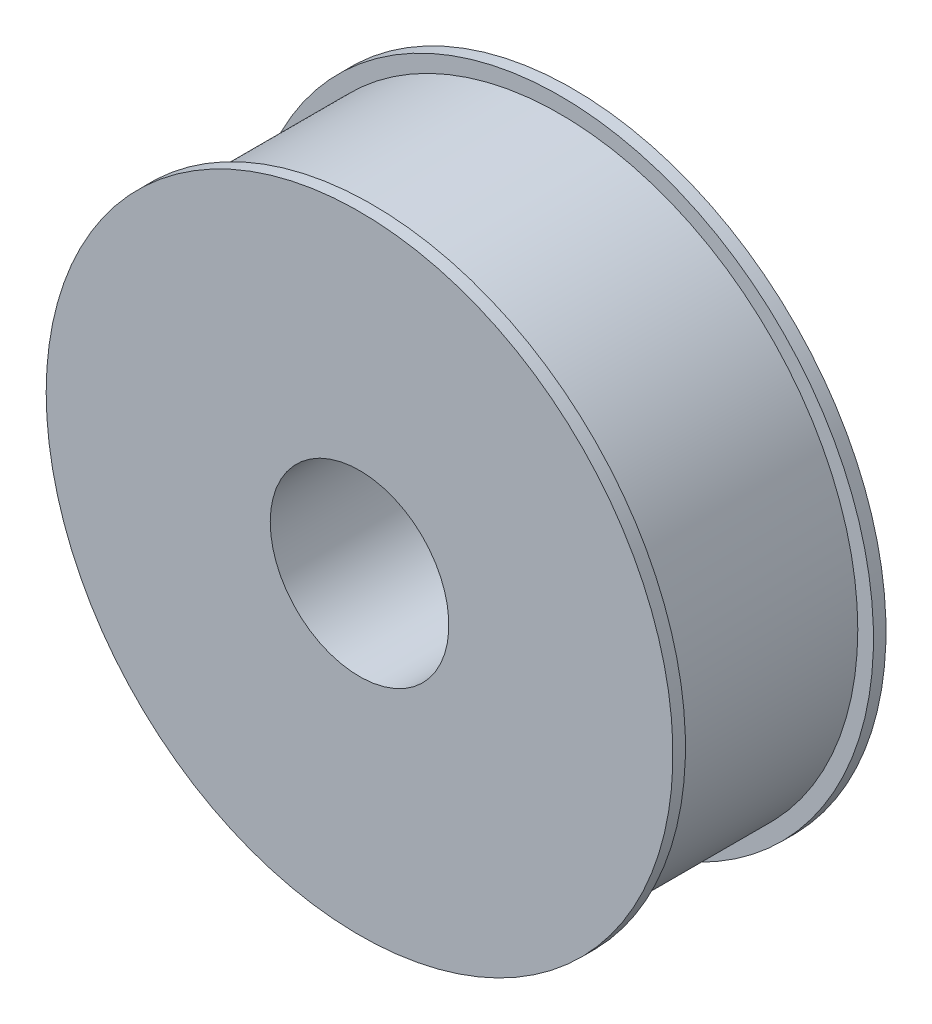
SolidWorks part; units mm, degrees
ref_plane "Front Plane" through (0, 0, 0) normal (0, 0, 1) x (1, 0, 0)
ref_plane "Top Plane" through (0, 0, 0) normal (0, 1, 0) x (1, 0, 0)
ref_plane "Right Plane" through (0, 0, 0) normal (1, 0, 0) x (0, 0, -1)
ref_plane "Plane1" through (0, 0, 0) normal (0, -1, 0) x (1, 0, 0)
sketch "Sketch1" plane through (0, 0, 0) normal (0, -1, 0) x (1, 0, 0)
  line L0 (28.5, 34) -> (28.5, -34)
  line L1 (28.5, -34) -> (100, -34)
  line L2 (100, -34) -> (100, -30)
  line L3 (100, -30) -> (95, -30)
  line L4 (95, -30) -> (95, 30)
  line L5 (95, 30) -> (100, 30)
  line L6 (100, 30) -> (100, 34)
  line L7 (100, 34) -> (28.5, 34)
  line L8 (0, 34) -> (0, -34) construction
revolve "Revolve1" add sketch "Sketch1" angle 360 about L8
